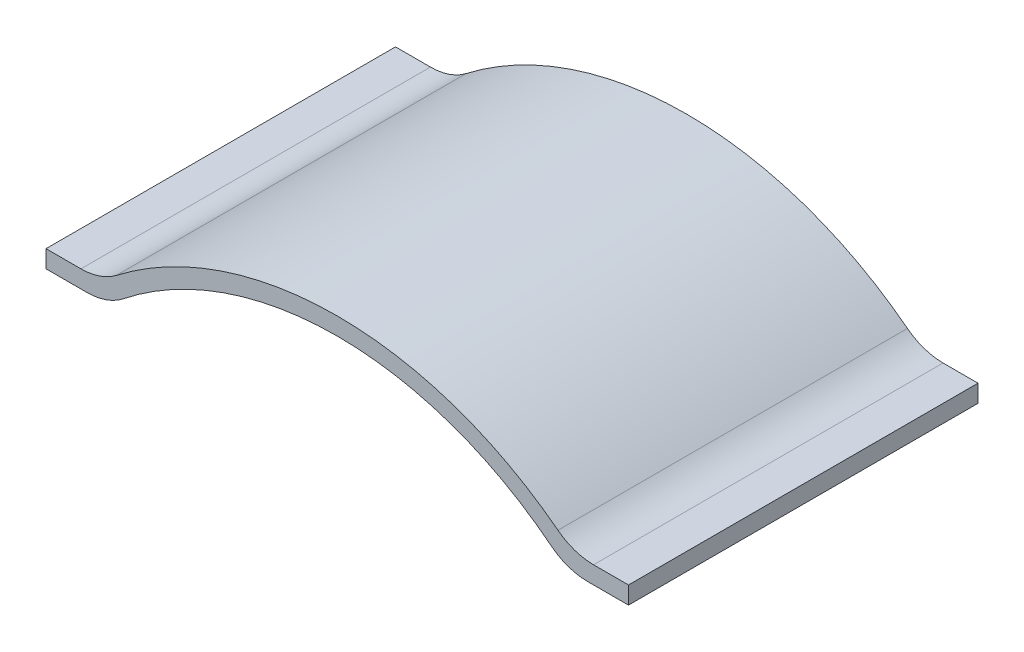
SolidWorks part; units mm, degrees
ref_plane "Front Plane" through (0, 0, 0) normal (0, 0, 1) x (1, 0, 0)
ref_plane "Top Plane" through (0, 0, 0) normal (0, 1, 0) x (1, 0, 0)
ref_plane "Right Plane" through (0, 0, 0) normal (1, 0, 0) x (0, 0, -1)
sketch "Sketch1" plane through (0, 0, 0) normal (0, 0, 1) x (1, 0, 0)
  line L0 (0, 0) -> (0, -3)
  line L1 (0, -3) -> (7.0349, -3)
  line L2 (0, 0) -> (6, 0)
  line L3 (50, -47.0333) -> (50, 15) construction
  line L4 (100, 0) -> (94, 0)
  line L5 (100, -3) -> (92.9651, -3)
  line L6 (100, 0) -> (100, -3)
  arc A1 (86.7413, -0.8271) -> (13.2587, -0.8271) centre (50, -47.0333) ccw
  arc A2 (87.8917, 2.0824) -> (12.1083, 2.0824) centre (50, -47.0333) ccw
  arc A3 (92.9651, -3) -> (86.7413, -0.8271) centre (92.9651, 7) cw
  arc A4 (94, 0) -> (87.8917, 2.0824) centre (94, 10) cw
  arc A5 (7.0349, -3) -> (13.2587, -0.8271) centre (7.0349, 7) ccw
  arc A6 (6, 0) -> (12.1083, 2.0824) centre (6, 10) ccw
  point P3 (50, 12)
  point P14 (89.3192, -3)
  point P17 (90.4475, 0)
  point P20 (10.6808, -3)
  point P23 (9.5525, 0)
  point P24 (159.576, -3)
  dimension "D2" = 3
  dimension "D3" = 10
  dimension "D5" = 15
  dimension "D1" = 3
  dimension "D4" = 6
  dimension "D6" = 100
extrude "Boss-Extrude1" add sketch "Sketch1" along normal blind 60
